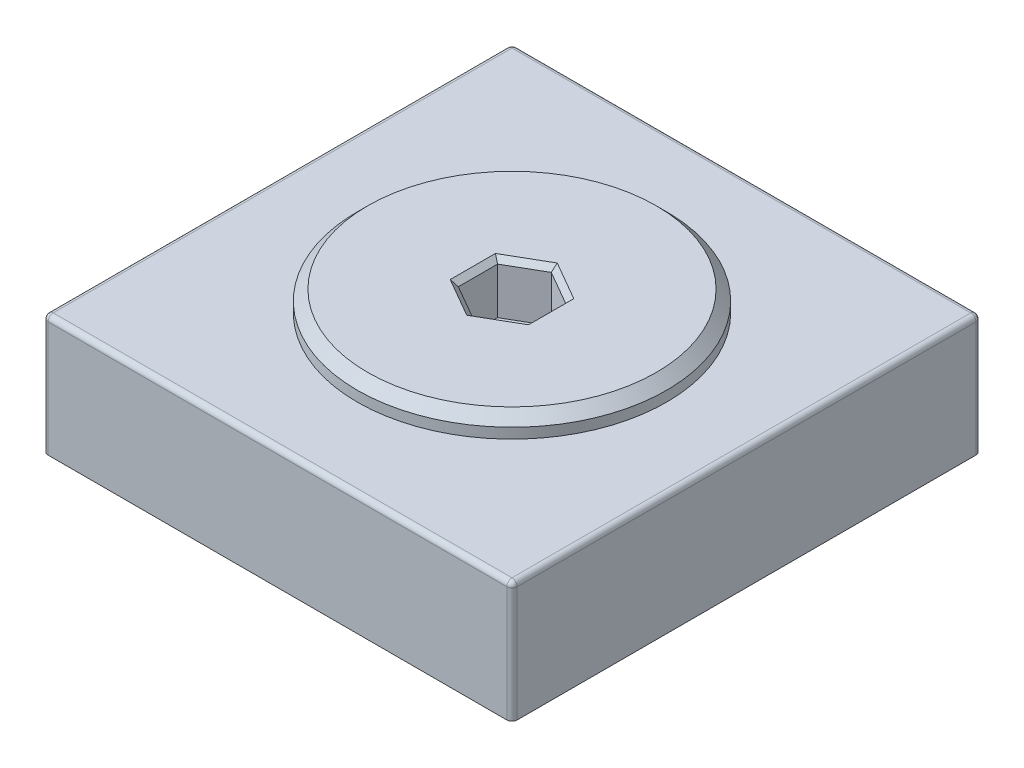
SolidWorks part; units mm, degrees
ref_plane "Front Plane" through (0, 0, 0) normal (0, 0, 1) x (1, 0, 0)
ref_plane "Top Plane" through (0, 0, 0) normal (0, 1, 0) x (1, 0, 0)
ref_plane "Right Plane" through (0, 0, 0) normal (1, 0, 0) x (0, 0, -1)
sketch "Sketch1" plane through (0, 0, 0) normal (0, 1, 0) x (1, 0, 0)
  line L1 (-22.75, -22.75) -> (22.75, -22.75)
  line L2 (-22.75, -22.75) -> (-22.75, 22.75)
  line L3 (-22.75, 22.75) -> (22.75, 22.75)
  line L4 (22.75, -22.75) -> (22.75, 22.75)
  line L5 (-22.75, -22.75) -> (22.75, 22.75) construction
  line L6 (-22.75, 22.75) -> (22.75, -22.75) construction
  point P0 (0, 0)
extrude "Boss-Extrude1" add sketch "Sketch1" along normal blind 11.7
sketch "Sketch2" plane through (0, 11.7, 0) normal (0, 1, 0) x (1, 0, 0)
  circle A0 centre (0, 0) radius 15
extrude "Boss-Extrude2" add sketch "Sketch2" along normal blind 2
chamfer "Chamfer1" distance 1 angle 45 1 edges at (0, 13.7, 15)
sketch "Sketch3" plane through (0, 13.7, 0) normal (0, 1, 0) x (1, 0, 0)
  line L1 (0, 3.8105) -> (-3.3, 1.9053)
  line L2 (-3.3, 1.9053) -> (-3.3, -1.9053)
  line L3 (-3.3, -1.9053) -> (0, -3.8105)
  line L4 (0, -3.8105) -> (3.3, -1.9053)
  line L5 (3.3, -1.9053) -> (3.3, 1.9053)
  line L6 (3.3, 1.9053) -> (0, 3.8105)
  circle A0 centre (0, 0) radius 3.3 construction
extrude "Cut-Extrude1" cut sketch "Sketch3" against normal blind 5
chamfer "Chamfer2" distance 0.5 angle 45 6 edges at (-1.65, 13.7, -2.8579) (-3.3, 13.7, 0) (-1.65, 13.7, 2.8579) (1.65, 13.7, 2.8579) (3.3, 13.7, 0) (1.65, 13.7, -2.8579)
fillet "Fillet1" radius 0.5 8 edges at (22.75, 5.85, -22.75) (-22.75, 5.85, -22.75) (22.75, 5.85, 22.75) (-22.75, 5.85, 22.75) (-22.75, 11.7, 0) (0, 11.7, -22.75) (22.75, 11.7, 0) (0, 11.7, 22.75)
sketch "Sketch4" plane through (0, 0, 0) normal (0, -1, 0) x (-1, 0, 0)
  circle A0 centre (0, 0) radius 15
extrude "Boss-Extrude3" add sketch "Sketch4" along normal blind 5
